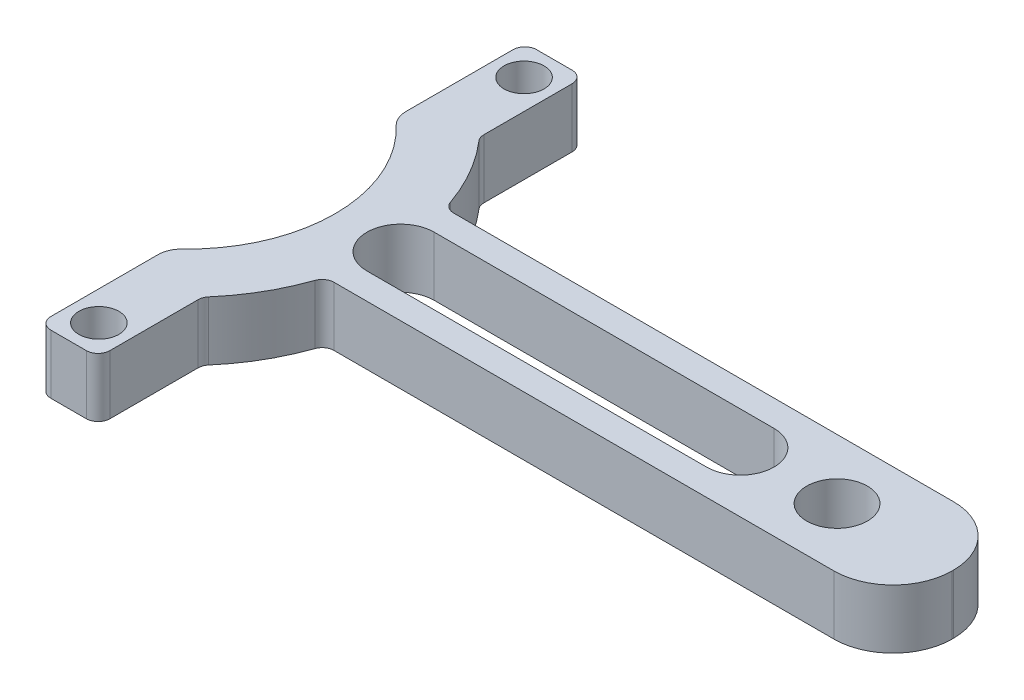
SolidWorks part; units mm, degrees
material "6061-T6 (SS)"
ref_plane "Front Plane" through (0, 0, 0) normal (0, 0, 1) x (1, 0, 0)
ref_plane "Top Plane" through (0, 0, 0) normal (0, 1, 0) x (1, 0, 0)
ref_plane "Right Plane" through (0, 0, 0) normal (1, 0, 0) x (0, 0, -1)
sketch "Sketch1" plane through (0, 0, 0) normal (0, 1, 0) x (1, 0, 0)
  circle A0 centre (0, 0) radius 15.875
  circle A1 centre (0, 0) radius 22.225
  dimension "D1" = 31.75
  dimension "D2" = 44.45
extrude "Boss-Extrude1" add sketch "Sketch1" along normal blind 6.35
sketch "Sketch2" plane through (0, 6.35, 0) normal (0, 1, 0) x (1, 0, 0)
  line L0 (75.9534, -6.4389) -> (38.5188, -6.4389)
  line L1 (82.3034, -0.0889) -> (82.3034, 0.0889)
  line L3 (75.9534, 6.4389) -> (38.5188, 6.4389)
  line L4 (82.3034, -6.4389) -> (38.5188, 6.4389) construction
  line L5 (38.5188, -6.4389) -> (82.3034, 6.4389) construction
  line L6 (38.5188, 6.4389) -> (17.5908, 6.4389)
  line L7 (60.4111, 0) -> (0, 0) construction
  line L11 (38.5188, -6.4389) -> (17.5908, -6.4389)
  line L12 (17.5908, 6.4389) -> (17.5908, -6.4389)
  arc A0 (82.3034, -0.0889) -> (75.9534, -6.4389) centre (75.9534, -0.0889) cw
  arc A1 (82.3034, 0.0889) -> (75.9534, 6.4389) centre (75.9534, 0.0889) ccw
  point P1 (60.4111, 0)
  point P2 (22.6571, 0)
  point P17 (26.3954, 0)
  point P26 (0, 0)
  point P27 (59.0105, 0)
  point P28 (0, 0)
  point P29 (0, 0)
  point P30 (21.2718, -6.4389)
  point P31 (0, 0)
  point P32 (0, 0)
  point P33 (0, 0)
  point P34 (0, 0)
  point P35 (0, 0)
  point P36 (21.2718, 6.4389)
  point P37 (0, 0)
  dimension "D4" = 6.35
  dimension "D3" = 12.8778
extrude "Boss-Extrude2" add sketch "Sketch2" against normal blind 6.35
hole_wizard "F (0.257) Diameter Hole1" positions "Sketch3" profile "Sketch4" hole size "F" standard "ANSI Inch" end condition through all
sketch "Sketch3" plane through (0, 6.35, 0) normal (0, 1, 0) x (1, 0, 0)
  line L0 (0, 0) -> (69.85, 0) construction
  point P0 (69.85, 0)
  dimension "D1" = 69.85
sketch "Sketch4" plane through (69.85, 6.35, 0) normal (1, 0, 0) x (0, 0, 1)
  line L0 (0, 0) -> (0, 6.35)
  line L1 (0, 6.35) -> (3.2639, 6.35)
  line L2 (3.2639, 6.35) -> (3.2639, 0)
  line L5 (3.2639, 0) -> (0, 0)
  line L11 (0, -6.35) -> (0, 107.95) construction
  dimension "Thru Hole Dia." = 6.5278
  dimension "Thru Hole Depth" = 6.35
sketch "Sketch6" plane through (0, 6.35, 0) normal (0, 1, 0) x (1, 0, 0)
  line L0 (10.16, 0) -> (15.875, 0) construction
  line L1 (10.16, -42.2389) -> (10.16, 39.9322)
  line L2 (10.16, -42.2389) -> (-55.3924, -42.2389)
  line L3 (10.16, 39.9322) -> (-55.3924, 39.9322)
  line L4 (-55.3924, -42.2389) -> (-55.3924, 39.9322)
  circle A1 centre (0, 0) radius 15.875 construction
  point P9 (0, 0)
  point P10 (0, 0)
  point P11 (3.0799, 0)
  dimension "D1" = 5.715
extrude "Cut-Extrude2" cut sketch "Sketch6" against normal through all
fillet "Fillet2" radius 2.54 2 edges at (10.16, 3.175, 12.198) (10.16, 3.175, -12.198)
sketch "Sketch9" plane through (0, 6.35, 0) normal (0, 1, 0) x (1, 0, 0)
  line L0 (10.16, 19.7668) -> (10.16, 26.1168)
  line L1 (10.16, 26.1168) -> (16.51, 26.1168)
  line L2 (16.51, 26.1168) -> (16.51, 14.8785)
  line L3 (10.16, 19.7668) -> (16.51, 14.8785)
  arc A0 (21.2718, 6.4389) -> (10.16, 19.7668) centre (0, 0) ccw construction
  circle A1 centre (13.335, 22.86) radius 2.1526
  point P3 (0, 0)
  point P10 (12.3681, 22.996)
  dimension "D4" = 4.3053
  dimension "D1" = 6.35
  dimension "D2" = 6.35
  dimension "D3" = 22.86
  dimension "D5" = 13.335
extrude "Boss-Extrude3" add sketch "Sketch9" against normal blind 6.35
mirror "Mirror1" about plane through (0, 0, 0) normal (0, 0, 1) of "Boss-Extrude3"
fillet "Fillet4" radius 1.27 8 edges at (21.2718, 3.175, 6.4389) (21.2718, 3.175, -6.4389) (16.51, 3.175, -14.8785) (16.51, 3.175, 14.8785) (16.51, 3.175, 26.1168) (10.16, 3.175, 26.1168) (16.51, 3.175, -26.1168) (10.16, 3.175, -26.1168)
sketch "Sketch11" plane through (0, 6.35, 0) normal (0, 1, 0) x (1, 0, 0)
  line L0 (59.4458, 0) -> (22.9162, 0) construction
  line L1 (59.4458, -3.6155) -> (22.9162, -3.6155)
  line L2 (59.4458, 3.6155) -> (22.9162, 3.6155)
  line L3 (15.875, 0) -> (64.7315, 0) construction
  arc A0 (59.4458, -3.6155) -> (59.4458, 3.6155) centre (59.4458, 0) ccw
  arc A1 (22.9162, 3.6155) -> (22.9162, -3.6155) centre (22.9162, 0) ccw
  arc A2 (10.9483, -11.4957) -> (10.9483, 11.4957) centre (0, 0) ccw construction
  point P2 (41.181, 0)
  point P13 (39.8448, 0)
  point P14 (59.4458, 0)
extrude "Cut-Extrude3" cut sketch "Sketch11" against normal through all
